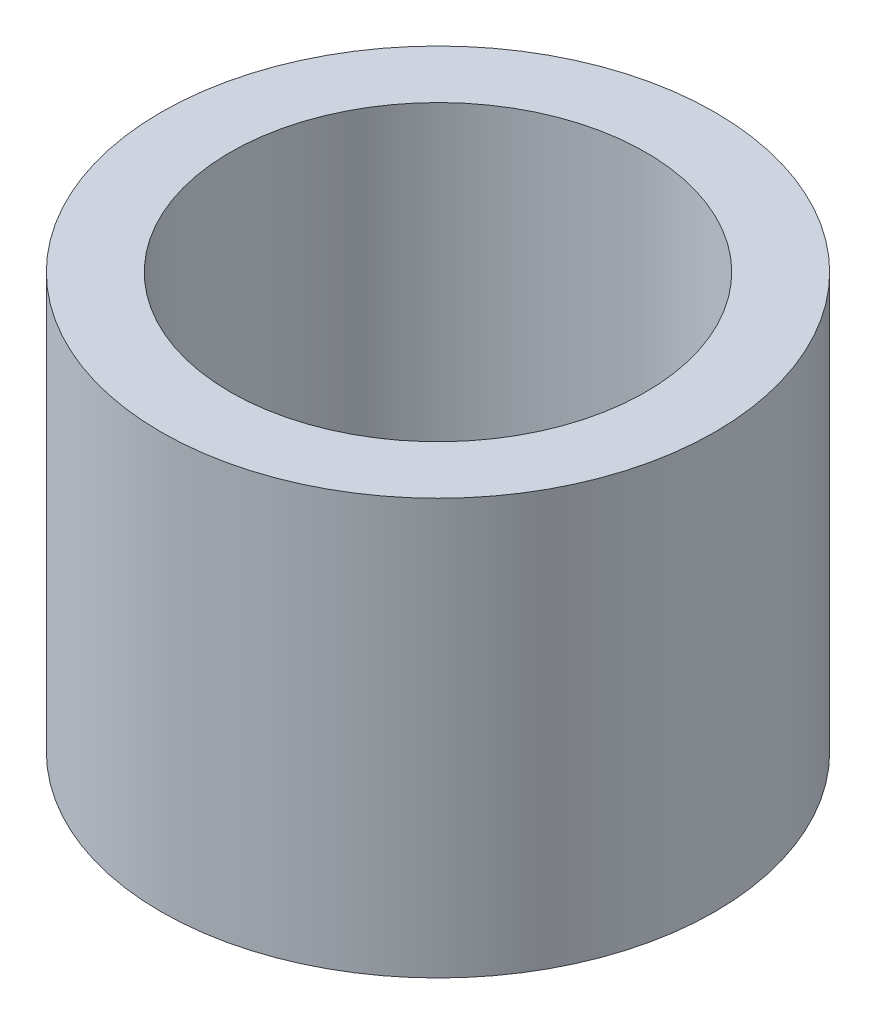
SolidWorks part; units mm, degrees
ref_plane "Front" through (0, 0, 0) normal (0, 0, 1) x (1, 0, 0)
ref_plane "Top" through (0, 0, 0) normal (0, 1, 0) x (1, 0, 0)
ref_plane "Right" through (0, 0, 0) normal (1, 0, 0) x (0, 0, -1)
sketch "Sketch1" plane through (0, 0, 0) normal (0, 1, 0) x (1, 0, 0)
  circle A0 centre (0, 0) radius 25.4
  circle A1 centre (0, 0) radius 19.05
  dimension "D1" = 50.8
  dimension "D2" = 38.1
extrude "Boss-Extrude1" add sketch "Sketch1" along normal blind 38.1
